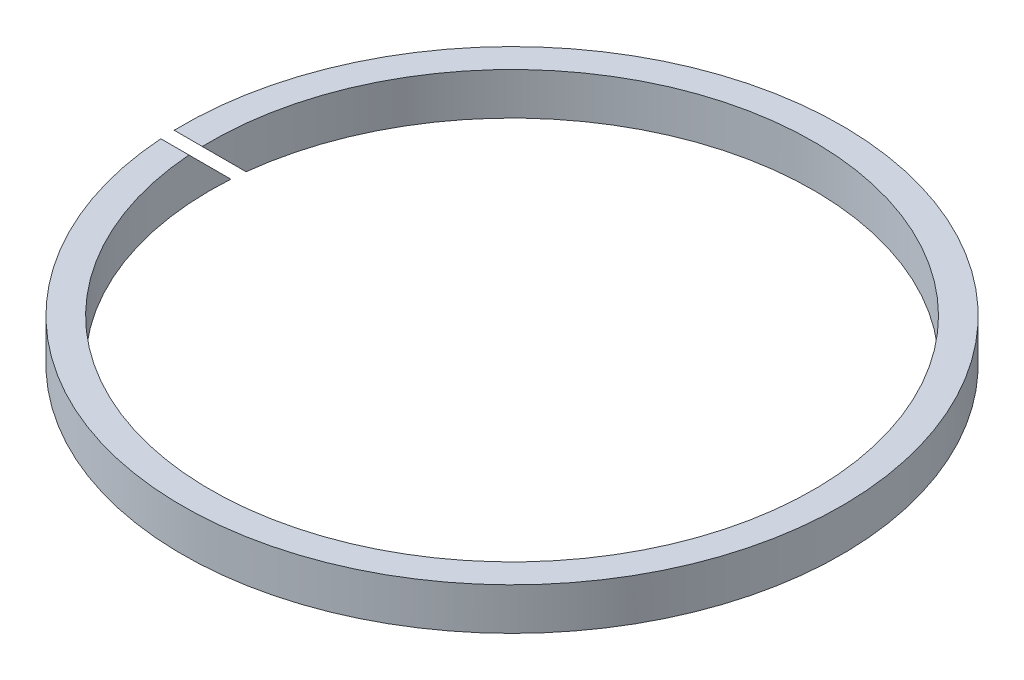
SolidWorks part; units mm, degrees
ref_plane "Front Plane" through (0, 0, 0) normal (0, 0, 1) x (1, 0, 0)
ref_plane "Top Plane" through (0, 0, 0) normal (0, 1, 0) x (1, 0, 0)
ref_plane "Right Plane" through (0, 0, 0) normal (1, 0, 0) x (0, 0, -1)
sketch "Sketch1" plane through (0, 0, 0) normal (0, 1, 0) x (1, 0, 0)
  circle A0 centre (0, 0) radius 21.5
  circle A1 centre (0, 0) radius 23.5
  dimension "D1" = 43
  dimension "D2" = 47
extrude "Boss-Extrude1" add sketch "Sketch1" along normal mid plane 3
sketch "Sketch2" plane through (0, 0, 0) normal (1, 0, 0) x (0, 0, -1)
  line L0 (-1.5937, 1.5) -> (1.4063, -1.5)
  line L1 (1.4063, -1.5) -> (2.4063, -1.5)
  line L2 (2.4063, -1.5) -> (-0.5937, 1.5)
  line L3 (-0.5937, 1.5) -> (-1.5937, 1.5)
  line L4 (0, 0) -> (0, 12.7852) construction
  line L5 (23.5, 1.5) -> (-23.5, 1.5) construction
  line L6 (21.5, 1.5) -> (-21.5, 1.5) construction
  line L7 (-23.5, -1.5) -> (23.5, -1.5) construction
  point P7 (0, 0)
  point P8 (-0.6659, 1.5)
  point P11 (-1.6974, 1.5)
  point P14 (2.4063, -1.5)
  dimension "D1" = 1
  dimension "D2" = 45
extrude "Cut-Extrude1" cut sketch "Sketch2" against normal up to next
